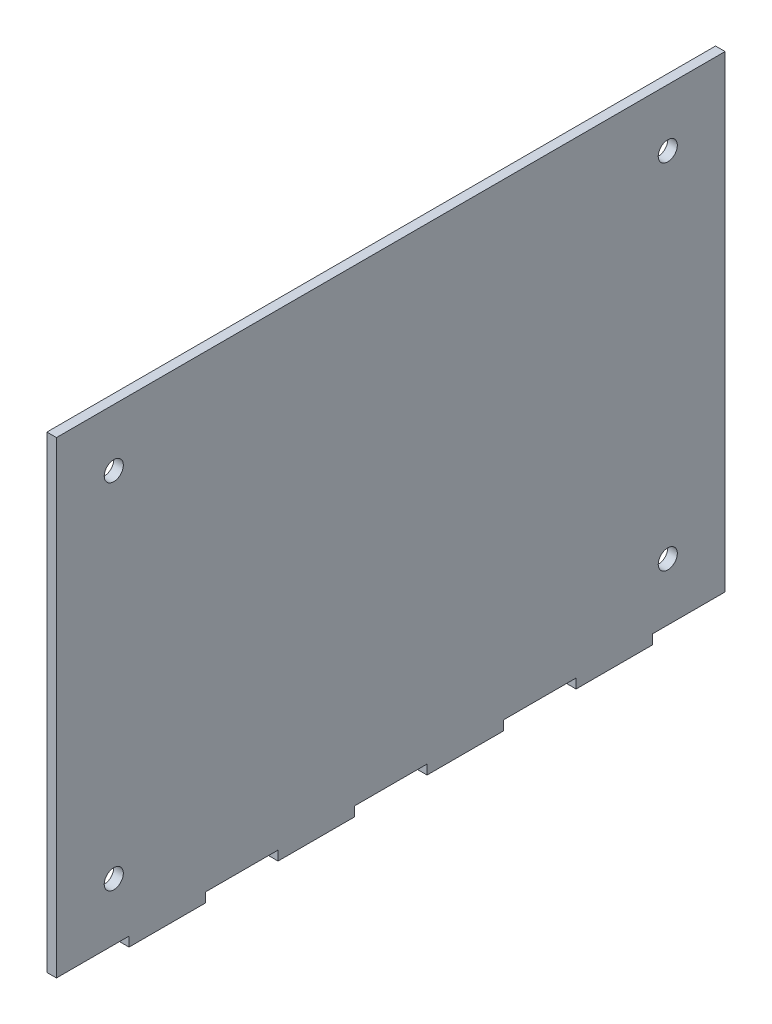
SolidWorks part; units mm, degrees
ref_plane "Front" through (0, 0, 0) normal (0, 0, 1) x (1, 0, 0)
ref_plane "Top" through (0, 0, 0) normal (0, 1, 0) x (1, 0, 0)
ref_plane "Right" through (0, 0, 0) normal (1, 0, 0) x (0, 0, -1)
sketch "Skizze1" plane through (0, 0, 0) normal (1, 0, 0) x (0, 0, -1)
  line L0 (175, 0) -> (-175, 0)
  line L1 (-175, 0) -> (-175, 250)
  line L2 (-175, 250) -> (175, 250)
  line L3 (0, 250) -> (0, 0) construction
  line L4 (175, 0) -> (175, 250)
  dimension "D1" = 350
  dimension "D2" = 250
extrude "Grundplatte" add sketch "Skizze1" along normal blind 5
sketch "Skizze2" plane through (5, 0, 0) normal (1, 0, 0) x (0, 0, -1)
  line L5 (-175, 0) -> (175, 0) construction
  line L11 (-175, 0) -> (-137, 0)
  line L12 (-175, 0) -> (-175, 5)
  line L13 (-175, 5) -> (-137, 5)
  line L14 (0, 0) -> (0, 250) construction
  line L15 (175, 250) -> (-175, 250) construction
  line L16 (-137, 0) -> (-137, 5)
  line L17 (-97, 0) -> (-59, 0)
  line L26 (-97, 0) -> (-97, 5)
  line L27 (-97, 5) -> (-59, 5)
  line L28 (-59, 0) -> (-59, 5)
  line L29 (-137, 5) -> (-97, 5) construction
  line L30 (-59, 5) -> (-19, 5) construction
  line L31 (19, 0) -> (-19, 0)
  line L32 (-19, 0) -> (-19, 5)
  line L34 (19, 0) -> (19, 5)
  line L35 (59, 5) -> (19, 5) construction
  line L36 (137, 5) -> (97, 5) construction
  line L37 (59, 0) -> (59, 5)
  line L38 (97, 5) -> (59, 5)
  line L39 (97, 0) -> (97, 5)
  line L40 (97, 0) -> (59, 0)
  line L41 (137, 0) -> (137, 5)
  line L42 (175, 5) -> (137, 5)
  line L43 (175, 0) -> (175, 5)
  line L44 (175, 0) -> (137, 0)
  line L45 (-19, 5) -> (0, 5) construction
  line L46 (-19, 5) -> (19, 5)
  point P14 (0, 7.2519)
  dimension "D1" = 40
  dimension "D2" = 5
extrude "Zapfen Boden" cut sketch "Skizze2" against normal through all
sketch "Skizze3" plane through (5, 0, 0) normal (1, 0, 0) x (0, 0, -1)
  line L0 (175, 5) -> (175, 250) construction
  line L1 (175, 250) -> (-175, 250) construction
  line L2 (0, 250) -> (0, 0) construction
  line L3 (-175, 127.5) -> (175, 127.5) construction
  line L4 (-175, 250) -> (-175, 5) construction
  circle A0 centre (145, 220) radius 5
  circle A1 centre (-145, 220) radius 5
  circle A2 centre (-145, 35) radius 5
  circle A3 centre (145, 35) radius 5
  dimension "D1" = 10
  dimension "D2" = 30
  dimension "D3" = 30
extrude "Verbindungsbohrungen" cut sketch "Skizze3" against normal through all
sketch "Skizze4" plane through (5, 0, 0) normal (1, 0, 0) x (0, 0, -1)
  line L0 (175, 127.5) -> (-175, 127.5) construction
  line L1 (175, 5) -> (175, 250) construction
  line L2 (-175, 250) -> (-175, 5) construction
  line L3 (170, 177.5) -> (170, 77.5)
  line L28 (175, 5) -> (170, 5)
  line L29 (175, 5) -> (175, 37.5)
  line L30 (175, 37.5) -> (170, 37.5)
  line L31 (170, 5) -> (170, 37.5)
  line L32 (170, 77.5) -> (175, 77.5)
  line L33 (175, 5) -> (175, 250) construction
  line L34 (175, 77.5) -> (175, 177.5)
  line L35 (170, 177.5) -> (175, 177.5)
  line L36 (170, 250) -> (170, 217.5)
  line L37 (175, 217.5) -> (170, 217.5)
  line L38 (175, 250) -> (175, 217.5)
  line L39 (175, 250) -> (170, 250)
  point P18 (170, 127.5)
  dimension "D1" = 5
  dimension "D2" = 40
  dimension "D3" = 100
extrude "Zapfen Seite" [suppressed] cut sketch "Skizze4" against normal through all
sketch "Skizze5" [suppressed] plane through (0, 0, 0) normal (-1, 0, 0) x (0, 0, 1)
  line L0 (0, 300) -> (0, 0) construction
  line L1 (-200, 300) -> (200, 300) construction
  line L2 (-200, 5) -> (-152, 5) construction
  line L3 (-200, 300) -> (-195, 300)
  line L4 (-200, 300) -> (-200, 5)
  line L5 (-200, 5) -> (-195, 5)
  line L6 (-195, 300) -> (-195, 5)
  dimension "D1" = 5
extrude "5mm Wandstärke Entfernnung" [suppressed] cut sketch "Skizze5" against normal through all
sketch "Skizze7" [suppressed] plane through (0, 0, 0) normal (-1, 0, 0) x (0, 0, 1)
  line L0 (-195, 5) -> (-195, 300) construction
  line L1 (-195, 300) -> (-200, 300)
  line L2 (-195, 300) -> (-195, 242.5)
  line L3 (-195, 242.5) -> (-200, 242.5)
  line L4 (-200, 300) -> (-200, 242.5)
  line L5 (-195, 202.5) -> (-200, 202.5)
  line L6 (-195, 202.5) -> (-195, 102.5)
  line L7 (-195, 102.5) -> (-200, 102.5)
  line L8 (-200, 202.5) -> (-200, 102.5)
  line L9 (-200, 152.5) -> (200, 152.5) construction
  line L10 (-195, 5) -> (-200, 5)
  line L11 (-195, 5) -> (-195, 62.5)
  line L12 (-195, 62.5) -> (-200, 62.5)
  line L13 (-200, 5) -> (-200, 62.5)
  line L14 (200, 300) -> (200, 5) construction
  dimension "D1" = 5
  dimension "D2" = 40
  dimension "D3" = 100
extrude "Aufsatz-Linear austragen2" [suppressed] add sketch "Skizze7" against normal up to surface (5 mm away)
sketch "Skizze8" plane through (5, 0, 0) normal (1, 0, 0) x (0, 0, -1)
  line L0 (175, 5) -> (175, 250) construction
  line L1 (175, 250) -> (170, 250)
  line L2 (175, 250) -> (175, 217.5)
  line L3 (175, 217.5) -> (170, 217.5)
  line L4 (170, 250) -> (170, 217.5)
  line L5 (175, 177.5) -> (170, 177.5)
  line L6 (175, 177.5) -> (175, 77.5)
  line L7 (175, 77.5) -> (170, 77.5)
  line L8 (170, 177.5) -> (170, 77.5)
  line L9 (175, 5) -> (137, 5) construction
  line L10 (175, 37.5) -> (170, 37.5)
  line L11 (175, 37.5) -> (175, 5)
  line L12 (175, 5) -> (170, 5)
  line L13 (170, 37.5) -> (170, 5)
  line L14 (170, 5) -> (170, 127.5) construction
  line L15 (170, 127.5) -> (170, 250) construction
  line L16 (0, 250) -> (0, 5) construction
  line L17 (175, 250) -> (-175, 250) construction
  line L18 (19, 5) -> (-19, 5) construction
  line L19 (-170, 127.5) -> (-170, 250) construction
  line L20 (-170, 5) -> (-170, 127.5) construction
  line L21 (-170, 37.5) -> (-170, 5)
  line L22 (-175, 5) -> (-170, 5)
  line L23 (-175, 37.5) -> (-175, 5)
  line L24 (-175, 37.5) -> (-170, 37.5)
  line L25 (-170, 177.5) -> (-170, 77.5)
  line L26 (-175, 77.5) -> (-170, 77.5)
  line L27 (-175, 177.5) -> (-175, 77.5)
  line L28 (-175, 177.5) -> (-170, 177.5)
  line L29 (-170, 250) -> (-170, 217.5)
  line L30 (-175, 217.5) -> (-170, 217.5)
  line L31 (-175, 250) -> (-175, 217.5)
  line L32 (-175, 250) -> (-170, 250)
  dimension "D1" = 5
  dimension "D2" = 40
  dimension "D3" = 100
extrude "Schnitt-Linear austragen1" [suppressed] cut sketch "Skizze8" against normal through all and the other way through all
sketch "Skizze9" [suppressed] plane through (5, 0, 0) normal (1, 0, 0) x (0, 0, -1)
  line L0 (170, 250) -> (-175, 250) construction
  line L1 (160, 250) -> (170, 250)
  line L2 (160, 250) -> (160, 208.6212)
  line L3 (160, 208.6212) -> (170, 208.6212)
  line L4 (170, 250) -> (170, 208.6212)
  line L5 (170, 5) -> (170, 250) construction
  line L6 (170, 5) -> (137, 5) construction
  line L7 (170, 168.6212) -> (160, 168.6212)
  line L8 (170, 168.6212) -> (170, 88.6212)
  line L9 (170, 88.6212) -> (160, 88.6212)
  line L10 (160, 168.6212) -> (160, 88.6212)
  line L11 (170, 46.3788) -> (160, 46.3788)
  line L12 (170, 46.3788) -> (170, 5)
  line L13 (170, 5) -> (160, 5)
  line L14 (160, 46.3788) -> (160, 5)
  line L15 (0, 5) -> (0, 250) construction
  line L17 (19, 5) -> (-19, 5) construction
  dimension "D1" = 10
  dimension "D2" = 40
  dimension "D3" = 80
extrude "Schnitt-Linear austragen2" [suppressed] cut sketch "Skizze9" against normal through all
